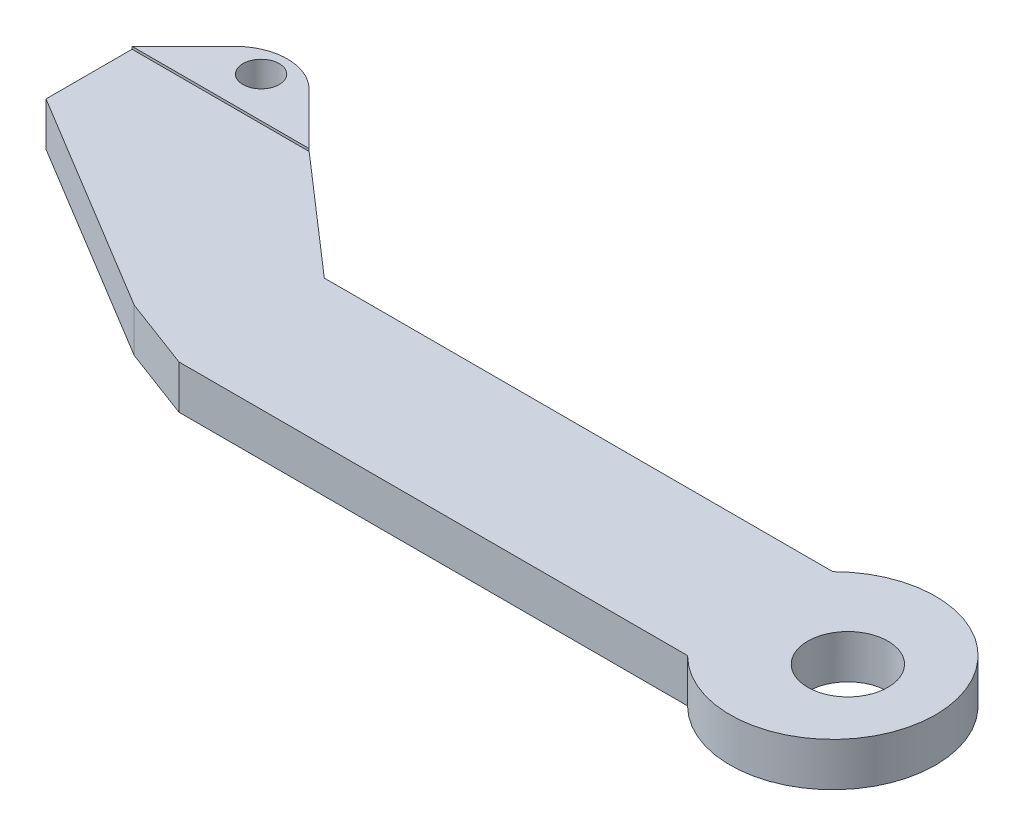
SolidWorks part; units mm, degrees
material "Acrylic (Medium-high impact)"
ref_plane "Front Plane" through (0, 0, 0) normal (0, 0, 1) x (1, 0, 0)
ref_plane "Top Plane" through (0, 0, 0) normal (0, 1, 0) x (1, 0, 0)
ref_plane "Right Plane" through (0, 0, 0) normal (1, 0, 0) x (0, 0, -1)
sketch "Sketch1" plane through (0, 0, 0) normal (0, 1, 0) x (1, 0, 0)
  line L0 (0, 0) -> (70, 0)
  line L1 (70, 0) -> (70, 20) construction
  line L2 (70, 20) -> (0, 20)
  line L3 (0, 20) -> (-16.1291, 34.0439)
  line L5 (0, 20) -> (0, 0) construction
  line L6 (-40.508, 22.1996) -> (-9.8501, 3.6874)
  line L7 (0, 20) -> (-9.8501, 3.6874) construction
  line L8 (-9.8501, 3.6874) -> (0, 0)
  line L9 (-40.508, 34.0439) -> (-16.1291, 34.0439)
  line L10 (70, 10) -> (80, 10) construction
  line L11 (-40.508, 34.0439) -> (-40.508, 22.1996)
  arc A0 (70, 20) -> (70, 0) centre (80, 10) cw
  dimension "D1" = 20
  dimension "D2" = 70
extrude "Boss-Extrude1" add sketch "Sketch1" along normal blind 6 contours L3 L9 L11 L6 L8 L0 A0 L2
sketch "Sketch2" plane through (0, 6, 0) normal (0, 1, 0) x (1, 0, 0)
  line L0 (70, 0) -> (70, 20) construction
  line L1 (70, 10) -> (94.1421, 10) construction
  arc A0 (70, 0) -> (70, 20) centre (80, 10) ccw construction
  circle A1 centre (82.0711, 10) radius 5.5179
extrude "Cut-Extrude1" cut sketch "Sketch2" against normal blind 6.35
sketch "Sketch4" plane through (0, 0, 0) normal (0, 1, 0) x (1, 0, 0)
  line L0 (-16.1291, 34.0439) -> (-23.2002, 41.115)
  line L1 (-40.508, 34.0439) -> (-33.4369, 41.115)
  line L2 (-16.1291, 34.0439) -> (-40.508, 34.0439)
  line L3 (-28.3185, 35.9966) -> (-28.3185, 43.2351) construction
  arc A0 (-23.2002, 41.115) -> (-33.4369, 41.115) centre (-28.3185, 35.9966) ccw
  circle A1 centre (-28.3185, 39.6158) radius 2.5
  dimension "D1" = 45
  dimension "D2" = 45
  dimension "D3" = 10
  dimension "D4" = 10
extrude "Boss-Extrude2" add sketch "Sketch4" along normal blind 6.35
